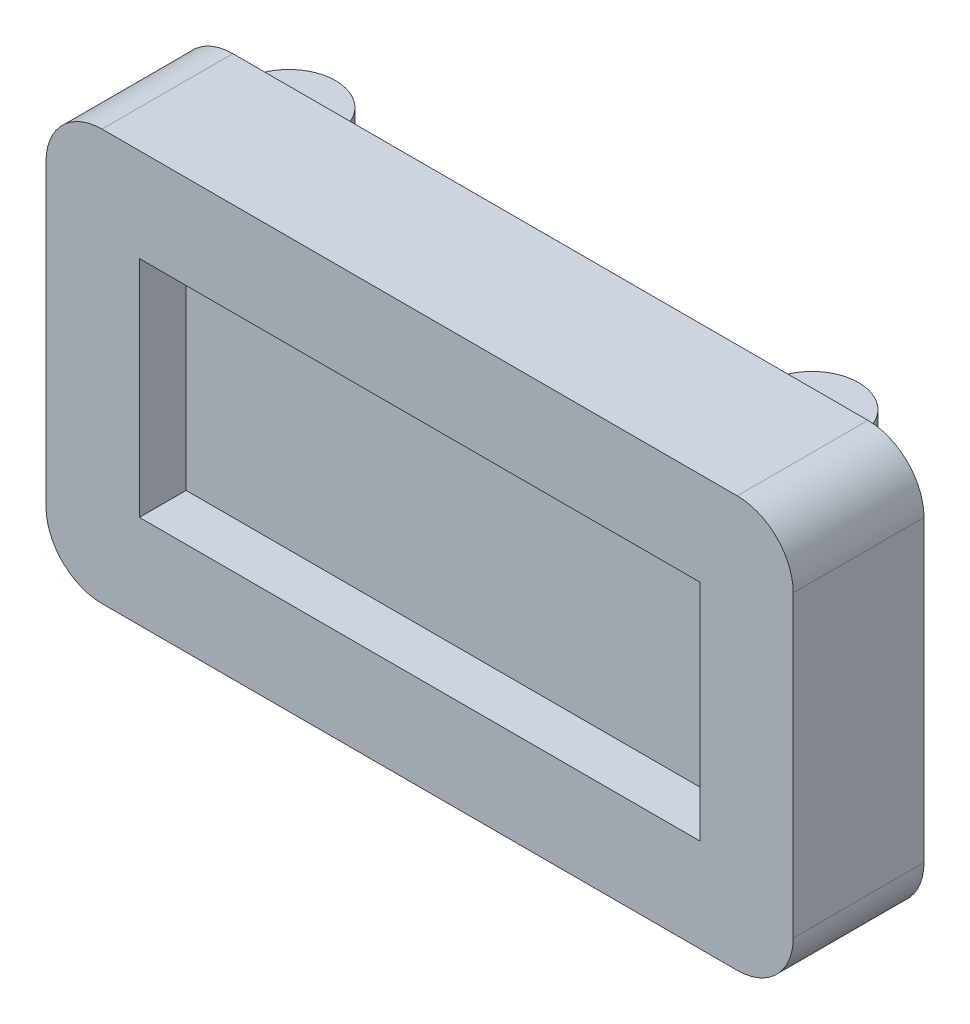
SolidWorks part; units mm, degrees
ref_plane "Front Plane" through (0, 0, 0) normal (0, 0, 1) x (1, 0, 0)
ref_plane "Top Plane" through (0, 0, 0) normal (0, 1, 0) x (1, 0, 0)
ref_plane "Right Plane" through (0, 0, 0) normal (1, 0, 0) x (0, 0, -1)
sketch "Sketch1" plane through (0, 0, 0) normal (0, 0, 1) x (1, 0, 0)
  line L1 (0, 0) -> (40, 0)
  line L2 (0, 0) -> (0, 22)
  line L3 (0, 22) -> (40, 22)
  line L4 (40, 0) -> (40, 22)
  dimension "D1" = 22
  dimension "D2" = 40
extrude "Boss-Extrude1" add sketch "Sketch1" along normal blind 7
fillet "Fillet1" radius 3 4 edges at (40, 0, 3.5) (0, 0, 3.5) (0, 22, 3.5) (40, 22, 3.5)
sketch "Sketch3" plane through (0, 0, 7) normal (0, 0, 1) x (1, 0, 0)
  line L8 (5, 5) -> (35, 5)
  line L9 (35, 5) -> (35, 17)
  line L10 (35, 17) -> (5, 17)
  line L11 (5, 17) -> (5, 5)
  line L12 (5, 5) -> (35, 5)
  line L13 (35, 5) -> (35, 17)
  line L14 (35, 17) -> (5, 17)
  line L15 (5, 17) -> (5, 5)
  dimension "D1" = 5
extrude "Cut-Extrude1" cut sketch "Sketch3" against normal blind 2.5
ref_plane "Plane1" through (0, 21, 0) normal (0, 1, 0) x (1, 0, 0)
sketch "Sketch4" plane through (0, 21, 0) normal (0, 1, 0) x (1, 0, 0)
  line L4 (37, 0) -> (3, 0)
  line L5 (3, 0) -> (3, -7)
  line L6 (3, -7) -> (37, -7)
  line L7 (37, -7) -> (37, 0)
  line L8 (37, 0) -> (3, 0)
  line L9 (3, 0) -> (3, -7)
  line L10 (3, -7) -> (37, -7)
  line L11 (37, -7) -> (37, 0)
  circle A0 centre (34, 0) radius 2.5
  circle A1 centre (6, 0) radius 2.5
  dimension "D2" = 5
  dimension "D3" = 5
  dimension "D4" = 3
  dimension "D5" = 3
  dimension "D1" = 0
extrude "Boss-Extrude2" add sketch "Sketch4" against normal blind 1 contours L8 A0 | L8 A1
ref_plane "Plane2" through (0, 11, 0) normal (0, -1, 0) x (-1, 0, 0)
mirror "Mirror1" about plane through (0, 11, 0) normal (0, -1, 0) of "Boss-Extrude2"
